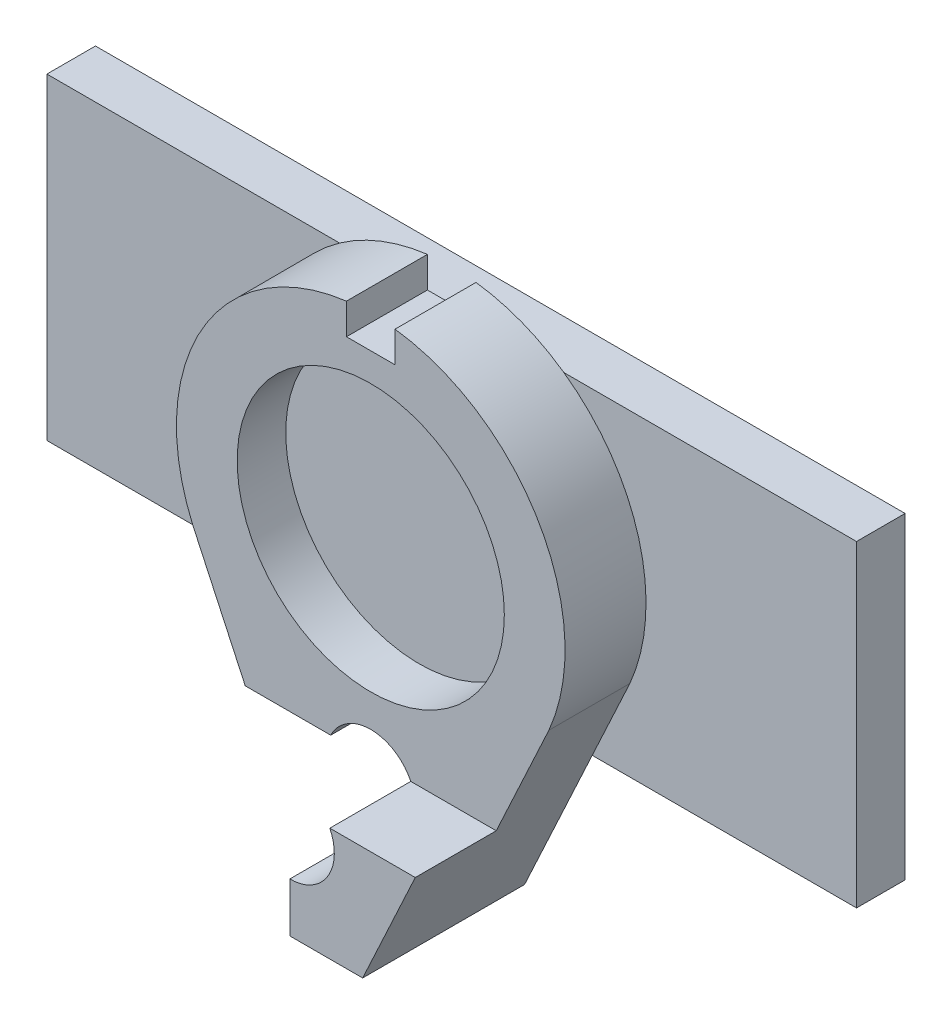
SolidWorks part; units mm, degrees
ref_plane "Plan de face" through (0, 0, 0) normal (0, 0, 1) x (1, 0, 0)
ref_plane "Plan de dessus" through (0, 0, 0) normal (0, 1, 0) x (1, 0, 0)
ref_plane "Plan de droite" through (0, 0, 0) normal (1, 0, 0) x (0, 0, -1)
sketch "Esquisse1" plane through (0, 0, 0) normal (0, 0, 1) x (1, 0, 0)
  line L0 (-11, -4.7958) -> (-4.5, -18.7958)
  line L1 (0, -55) -> (0, 55) construction
  line L2 (11, -4.7958) -> (4.5, -18.7958)
  line L3 (-4.5, -18.7958) -> (4.5, -18.7958)
  arc A0 (-11, -4.7958) -> (11, -4.7958) centre (0, 0) cw
  point P9 (-4.5, -18.7958)
  dimension "D2" = 12
  dimension "D1" = 22
  dimension "D4" = 9
  dimension "D5" = 14
extrude "Boss.-Extru.1" add sketch "Esquisse1" along normal blind 5
sketch "Esquisse2" plane through (0, 0, 5) normal (0, 0, 1) x (1, 0, 0)
  circle A0 centre (0, 0) radius 8.25
  dimension "D1" = 16.5
extrude "Enlèv. mat.-Extru.1" cut sketch "Esquisse2" against normal blind 3
ref_plane "Plan1" through (0, 12, 0) normal (0, 1, 0) x (1, 0, 0)
sketch "Esquisse4" plane through (0, 12, 0) normal (0, 1, 0) x (1, 0, 0)
  line L0 (1.5, -5) -> (1.5, 0)
  line L1 (1.5, -5) -> (-1.5, -5)
  line L2 (1.5, 0) -> (-1.5, 0)
  line L3 (-1.5, -5) -> (-1.5, 0)
  line L4 (1.5, -5) -> (-1.5, 0) construction
  line L5 (1.5, 0) -> (-1.5, -5) construction
  line L6 (12, 0) -> (-12, 0) construction
  point P0 (8.9418, 0)
  point P1 (0, -2.5)
  dimension "D1" = 3
  dimension "D2" = 5
extrude "Enlèv. mat.-Extru.2" cut sketch "Esquisse4" against normal blind 2 contours L0 L2 L3 L1
sketch "Esquisse6" plane through (0, 0, 5) normal (0, 0, 1) x (1, 0, 0)
  line L0 (0, -18.7958) -> (4.5, -18.7958)
  line L1 (-4.5, -18.7958) -> (4.5, -18.7958) construction
  line L2 (4.5, -18.7958) -> (7.75, -11.7958)
  line L3 (4.5, -18.7958) -> (11, -4.7958) construction
  line L4 (7.75, -11.7958) -> (0, -11.7958)
  line L5 (0, -11.7958) -> (0, -18.7958)
  dimension "D1" = 7
extrude "Boss.-Extru.2" add sketch "Esquisse6" along normal blind 5
sketch "Esquisse7" plane through (0, 0, 5) normal (0, 0, 1) x (1, 0, 0)
  line L0 (0, -18.7958) -> (0, -11.7958)
  line L1 (0, -11.7958) -> (-7.75, -11.7958)
  line L2 (-11, -4.7958) -> (-4.5, -18.7958) construction
  line L3 (-7.75, -11.7958) -> (-4.5, -18.7958)
  line L4 (-4.5, -18.7958) -> (0, -18.7958)
extrude "Enlèv. mat.-Extru.4" cut sketch "Esquisse7" against normal blind 5
sketch "Esquisse8" plane through (0, 0, 0) normal (0, 0, -1) x (-1, 0, 0)
  line L0 (25, 9.8) -> (-25, 9.8)
  line L1 (25, 9.8) -> (25, -9.8)
  line L2 (-25, 9.8) -> (-25, -9.8)
  line L3 (25, -9.8) -> (-25, -9.8)
  line L4 (25, 9.8) -> (-25, -9.8) construction
  line L5 (-25, 9.8) -> (25, -9.8) construction
  point P1 (0, 0)
  dimension "D1" = 50
  dimension "D2" = 19.6
extrude "Boss.-Extru.3" add sketch "Esquisse8" along normal blind 3
sketch "Esquisse10" plane through (0, 0, 5) normal (0, 0, 1) x (1, 0, 0)
  circle A0 centre (0, -13) radius 2.75
  point P2 (0, 0)
  dimension "D2" = 5.5
  dimension "D1" = 13
extrude "Enlèv. mat.-Extru.5" cut sketch "Esquisse10" against normal through all both and the other way through all
